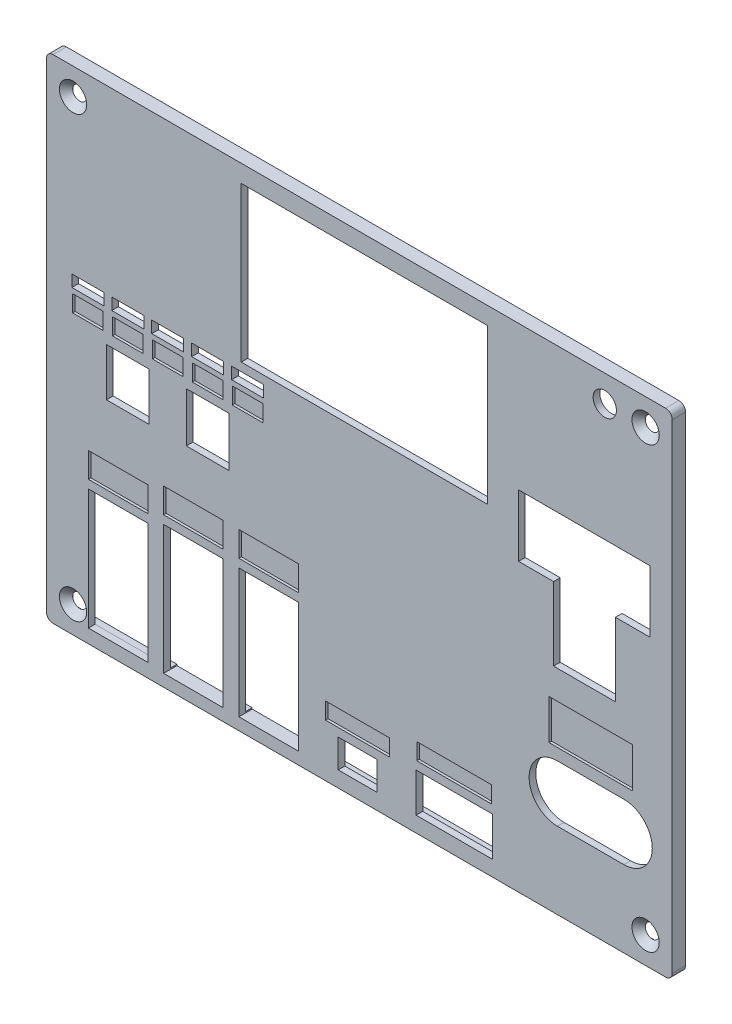
SolidWorks part; units mm, degrees
ref_plane "Alzado" through (0, 0, 0) normal (0, 0, 1) x (1, 0, 0)
ref_plane "Planta" through (0, 0, 0) normal (0, 1, 0) x (1, 0, 0)
ref_plane "Vista lateral" through (0, 0, 0) normal (1, 0, 0) x (0, 0, -1)
sketch "Croquis1" plane through (0, 0, 0) normal (0, 0, 1) x (1, 0, 0)
  line L1 (0, 0) -> (188, 0)
  line L2 (0, 0) -> (0, 148)
  line L3 (0, 148) -> (188, 148)
  line L4 (188, 0) -> (188, 148)
  dimension "D1" = 148
  dimension "D2" = 188
extrude "Saliente-Extruir1" add sketch "Croquis1" along normal blind 4
ref_plane "Plano1" through (0, 0, 0) normal (0, 0, -1) x (-1, 0, 0)
sketch "Croquis2" plane through (0, 0, 0) normal (0, 0, -1) x (-1, 0, 0)
  line L0 (-188, 148) -> (0, 148) construction
  line L1 (-180, 140) -> (-8, 140)
  line L2 (-180, 140) -> (-180, 8)
  line L3 (-180, 8) -> (-8, 8)
  line L4 (-8, 140) -> (-8, 8)
  line L5 (-188, 0) -> (-188, 148) construction
  line L6 (0, 0) -> (-188, 0) construction
  line L7 (0, 148) -> (0, 0) construction
  circle A0 centre (-8, 140) radius 2.1
  circle A1 centre (-180, 140) radius 2.1
  circle A2 centre (-180, 8) radius 2.1
  circle A3 centre (-8, 8) radius 2.1
  dimension "D5" = 4.2
  dimension "D6" = 4.2
  dimension "D7" = 4.2
  dimension "D8" = 4.2
  dimension "D1" = 8
  dimension "D2" = 8
  dimension "D3" = 8
  dimension "D4" = 8
extrude "Cortar-Extruir1" cut sketch "Croquis2" against normal blind 4 contours A0 | A1 | A2 | A3
fillet "Redondeo1" radius 2 4 edges at (0, 0, 2) (188, 0, 2) (188, 148, 2) (0, 148, 2)
chamfer "Chaflán1" distance 2 angle 45 4 edges at (5.9, 8, 4) (177.9, 8, 4) (177.9, 140, 4) (5.9, 140, 4)
sketch "Croquis3" plane through (0, 0, 0) normal (0, 0, -1) x (-1, 0, 0)
  line L0 (-184, 144) -> (-4, 144) construction
  line L1 (-4, 144) -> (-4, 4) construction
  line L2 (-4, 4) -> (-184, 4) construction
  line L3 (-184, 4) -> (-184, 144) construction
  line L4 (-186, 148) -> (-2, 148) construction
  line L5 (-188, 2) -> (-188, 146) construction
  line L6 (0, 146) -> (0, 2) construction
  line L7 (-2, 0) -> (-186, 0) construction
  dimension "D1" = 4
  dimension "D2" = 4
  dimension "D3" = 4
  dimension "D4" = 4
sketch "Croquis4" plane through (0, 0, 4) normal (0, 0, 1) x (1, 0, 0)
  line L0 (28.25, 93.27) -> (20.63, 93.27) construction
  line L1 (12.6, 40.31) -> (30.5, 40.31)
  line L2 (12.6, 40.31) -> (12.6, 4.11)
  line L3 (12.6, 4.11) -> (30.5, 4.11)
  line L4 (30.5, 40.31) -> (30.5, 4.11)
  line L5 (31.63, 93.77) -> (41.25, 93.77)
  line L6 (31.63, 93.77) -> (31.63, 90.23)
  line L7 (15.1, 5.61) -> (28, 5.61) construction
  line L8 (14.1, 31.91) -> (14.1, 6.61) construction
  line L9 (29, 6.61) -> (29, 37.81) construction
  line L10 (28, 38.81) -> (17.3, 38.81) construction
  line L11 (37.7, 5.13) -> (50.6, 5.13) construction
  line L12 (35.2, 42.37) -> (53.1, 42.37)
  line L13 (35.2, 42.37) -> (35.2, 3.63)
  line L14 (35.2, 3.63) -> (53.1, 3.63)
  line L15 (53.1, 42.37) -> (53.1, 3.63)
  line L16 (51.6, 6.13) -> (51.6, 39.87) construction
  line L17 (36.7, 33.97) -> (36.7, 6.13) construction
  line L18 (50.6, 40.87) -> (39.9, 40.87) construction
  line L19 (73.22, 40.87) -> (62.52, 40.87) construction
  line L20 (57.82, 42.37) -> (75.72, 42.37)
  line L21 (57.82, 42.37) -> (57.82, 3.63)
  line L22 (57.82, 3.63) -> (75.72, 3.63)
  line L23 (75.72, 42.37) -> (75.72, 3.63)
  line L24 (59.32, 8.58) -> (59.32, 39.87) construction
  line L25 (74.22, 6.13) -> (74.22, 39.87) construction
  line L26 (60.32, 5.13) -> (73.22, 5.13) construction
  line L27 (31.63, 90.23) -> (41.25, 90.23)
  line L28 (94.476, 11.27) -> (92.444, 11.27) construction
  line L29 (87.65, 13.27) -> (99.27, 13.27)
  line L30 (87.65, 13.27) -> (87.65, 4.73)
  line L31 (87.65, 4.73) -> (99.27, 4.73)
  line L32 (99.27, 13.27) -> (99.27, 4.73)
  line L33 (97.27, 8.984) -> (97.27, 11.016) construction
  line L34 (89.65, 11.016) -> (89.65, 8.984) construction
  line L35 (92.444, 8.73) -> (94.476, 8.73) construction
  line L36 (129.95, 9.5) -> (129.95, 13.4) construction
  line L37 (111.05, 16.4) -> (133.95, 16.4)
  line L38 (111.05, 16.4) -> (111.05, 4.65)
  line L39 (111.05, 4.65) -> (133.95, 4.65)
  line L40 (133.95, 16.4) -> (133.95, 4.65)
  line L41 (115.05, 13.4) -> (115.05, 9.5) construction
  line L42 (118.5, 7.65) -> (126.5, 7.65) construction
  line L43 (129.95, 13.4) -> (115.05, 13.4) construction
  line L44 (41.25, 93.77) -> (41.25, 90.23)
  line L45 (16.25, 93.27) -> (8.63, 93.27) construction
  line L46 (7.63, 93.77) -> (17.25, 93.77)
  line L47 (7.63, 93.77) -> (7.63, 90.23)
  line L48 (7.63, 90.23) -> (17.25, 90.23)
  line L49 (17.25, 93.77) -> (17.25, 90.23)
  line L50 (8.63, 90.73) -> (16.25, 90.73) construction
  line L51 (8.63, 93.27) -> (8.63, 90.73) construction
  line L52 (16.25, 90.73) -> (16.25, 93.27) construction
  line L53 (43.63, 93.77) -> (53.25, 93.77)
  line L54 (19.63, 93.77) -> (29.25, 93.77)
  line L55 (19.63, 93.77) -> (19.63, 90.23)
  line L56 (19.63, 90.23) -> (29.25, 90.23)
  line L57 (29.25, 93.77) -> (29.25, 90.23)
  line L58 (43.63, 93.77) -> (43.63, 90.23)
  line L59 (43.63, 90.23) -> (53.25, 90.23)
  line L60 (53.25, 93.77) -> (53.25, 90.23)
  line L61 (55.63, 93.77) -> (65.25, 93.77)
  line L62 (55.63, 93.77) -> (55.63, 90.23)
  line L63 (55.63, 90.23) -> (65.25, 90.23)
  line L64 (65.25, 93.77) -> (65.25, 90.23)
  line L65 (20.63, 93.27) -> (20.63, 90.73) construction
  line L66 (20.63, 90.73) -> (28.25, 90.73) construction
  line L67 (28.25, 90.73) -> (28.25, 93.27) construction
  line L68 (40.25, 93.27) -> (32.63, 93.27) construction
  line L69 (32.63, 93.27) -> (32.63, 90.73) construction
  line L70 (32.63, 90.73) -> (40.25, 90.73) construction
  line L71 (40.25, 90.73) -> (40.25, 93.27) construction
  line L72 (44.63, 93.27) -> (44.63, 90.73) construction
  line L73 (52.25, 93.27) -> (44.63, 93.27) construction
  line L74 (44.63, 90.73) -> (52.25, 90.73) construction
  line L75 (52.25, 90.73) -> (52.25, 93.27) construction
  line L76 (64.25, 93.27) -> (56.63, 93.27) construction
  line L77 (56.63, 93.27) -> (56.63, 90.73) construction
  line L78 (56.63, 90.73) -> (64.25, 90.73) construction
  line L79 (64.25, 90.73) -> (64.25, 93.27) construction
  line L80 (131.02, 141.25) -> (60.02, 141.25) construction
  line L81 (58.52, 142.75) -> (132.52, 142.75)
  line L82 (58.52, 142.75) -> (58.52, 96.25)
  line L83 (58.52, 96.25) -> (132.52, 96.25)
  line L84 (132.52, 142.75) -> (132.52, 96.25)
  line L85 (60.02, 141.25) -> (60.02, 97.75) construction
  line L86 (60.02, 97.75) -> (89.52, 97.75) construction
  line L87 (131.02, 97.75) -> (131.02, 141.25) construction
  line L88 (23.675, 79.6) -> (25.175, 79.6) construction
  line L89 (18.025, 80.6) -> (30.825, 80.6)
  line L90 (18.025, 80.6) -> (18.025, 66.2)
  line L91 (18.025, 66.2) -> (30.825, 66.2)
  line L92 (30.825, 80.6) -> (30.825, 66.2)
  line L93 (29.325, 75) -> (29.325, 70) construction
  line L94 (19.525, 70) -> (19.525, 75) construction
  line L95 (20.675, 67.7) -> (26.85, 67.7) construction
  line L96 (47.675, 79.6) -> (49.175, 79.6) construction
  line L97 (42.025, 81.1) -> (54.825, 81.1)
  line L98 (42.025, 81.1) -> (42.025, 66.2)
  line L99 (42.025, 66.2) -> (54.825, 66.2)
  line L100 (54.825, 81.1) -> (54.825, 66.2)
  line L101 (53.325, 75) -> (53.325, 70) construction
  line L102 (44.675, 67.7) -> (50.85, 67.7) construction
  line L103 (43.525, 70) -> (43.525, 75) construction
  line L105 (141.84, 104.68) -> (181.39, 104.68)
  line L109 (145.265, 103.18) -> (148.44, 103.18) construction
  line L112 (153.5, 31.5) -> (173.5, 31.5) construction
  line L113 (153.5, 31.5) -> (173.5, 31.5) construction
  line L114 (153.5, 40) -> (173.5, 40)
  line L115 (153.5, 23) -> (173.5, 23)
  line L116 (141.84, 104.68) -> (141.84, 86.08)
  line L117 (141.84, 86.08) -> (152.34, 86.08)
  line L118 (152.34, 86.08) -> (152.34, 64.08)
  line L119 (152.34, 64.08) -> (170.94, 64.08)
  line L120 (170.94, 64.08) -> (170.94, 86.08)
  line L121 (170.94, 86.08) -> (181.39, 86.08)
  line L122 (181.39, 86.08) -> (181.39, 104.68)
  line L123 (143.34, 102.38) -> (143.34, 101.18) construction
  line L124 (145.265, 87.58) -> (148.44, 87.58) construction
  line L125 (153.84, 80.38) -> (153.84, 79.18) construction
  line L126 (155.765, 65.58) -> (158.94, 65.58) construction
  line L127 (169.44, 79.18) -> (169.44, 80.38) construction
  line L128 (174.79, 87.58) -> (177.965, 87.58) construction
  line L129 (179.89, 89.58) -> (179.89, 88.38) construction
  arc A0 (153.5, 40) -> (153.5, 23) centre (153.5, 31.5) ccw
  arc A1 (173.5, 23) -> (173.5, 40) centre (173.5, 31.5) ccw
  circle A2 centre (167.73, 140) radius 3.5
  point P68 (12.44, 90.73)
  point P141 (18.025, 73.4)
  point P174 (163.5, 31.5)
  point P192 (176.3775, 87.58)
  dimension "D57" = 17
  dimension "D58" = 7
  dimension "D1" = 1.5
  dimension "D2" = 1.5
  dimension "D3" = 1.5
  dimension "D4" = 1.5
  dimension "D5" = 1.5
  dimension "D6" = 1.5
  dimension "D7" = 1.5
  dimension "D8" = 1.5
  dimension "D9" = 1.5
  dimension "D10" = 1.5
  dimension "D11" = 1.5
  dimension "D12" = 1.5
  dimension "D13" = 2
  dimension "D14" = 2
  dimension "D15" = 2
  dimension "D16" = 4
  dimension "D17" = 4
  dimension "D18" = 4
  dimension "D19" = 3
  dimension "D20" = 3
  dimension "D21" = 0.5
  dimension "D22" = 0.5
  dimension "D23" = 1
  dimension "D24" = 1
  dimension "D25" = 0.5
  dimension "D26" = 1
  dimension "D27" = 0.5
  dimension "D28" = 1
  dimension "D29" = 0.5
  dimension "D30" = 1
  dimension "D31" = 0.5
  dimension "D32" = 1
  dimension "D33" = 1
  dimension "D34" = 0.5
  dimension "D35" = 0.5
  dimension "D36" = 1
  dimension "D37" = 0.5
  dimension "D38" = 1
  dimension "D39" = 0.5
  dimension "D40" = 1
  dimension "D41" = 1.5
  dimension "D42" = 1.5
  dimension "D43" = 1.5
  dimension "D44" = 1.5
  dimension "D45" = 1
  dimension "D46" = 1.5
  dimension "D47" = 1.5
  dimension "D48" = 1.5
  dimension "D49" = 1.5
  dimension "D50" = 1.5
  dimension "D51" = 1.5
  dimension "D52" = 1.5
  dimension "D53" = 1.5
  dimension "D54" = 1.5
  dimension "D55" = 1.5
  dimension "D56" = 1.5
  dimension "D59" = 1.5
  dimension "D60" = 1.5
  dimension "D61" = 1.5
  dimension "D62" = 1.5
extrude "Cortar-Extruir4" cut sketch "Croquis4" against normal up to next
sketch "Croquis5" plane through (0, 0, 0) normal (0, 0, -1) x (-1, 0, 0)
  line L1 (-4, 144) -> (-184, 144)
  line L2 (-4, 144) -> (-4, 4)
  line L3 (-4, 4) -> (-184, 4)
  line L4 (-184, 144) -> (-184, 4)
extrude "Cortar-Extruir5" cut sketch "Croquis5" against normal blind 2
sketch "Croquis7" plane through (0, 0, 0) normal (0, 0, -1) x (-1, 0, 0)
  line L0 (0, 74) -> (-4, 74) construction
  line L1 (-186, 61.5) -> (-186, 86.5) construction
  line L3 (-2, 61.5) -> (-2, 86.5) construction
  line L6 (0, 146) -> (0, 2) construction
  line L7 (-4, 144) -> (-4, 4) construction
  line L8 (-188, 74) -> (-184, 74) construction
  line L9 (-188, 2) -> (-188, 146) construction
  line L10 (-184, 4) -> (-184, 144) construction
  line L16 (-186.5, 61.5) -> (-186.5, 86.5)
  line L17 (-185.5, 61.5) -> (-185.5, 86.5)
  line L18 (-2.5, 61.5) -> (-2.5, 86.5)
  line L19 (-1.5, 61.5) -> (-1.5, 86.5)
  arc A8 (-186.5, 61.5) -> (-185.5, 61.5) centre (-186, 61.5) ccw
  arc A9 (-185.5, 86.5) -> (-186.5, 86.5) centre (-186, 86.5) ccw
  arc A10 (-2.5, 61.5) -> (-1.5, 61.5) centre (-2, 61.5) ccw
  arc A11 (-1.5, 86.5) -> (-2.5, 86.5) centre (-2, 86.5) ccw
  point P8 (-2, 74)
  point P22 (-186, 74)
  dimension "D1" = 25
  dimension "D2" = 1
  dimension "D3" = 25
  dimension "D4" = 1
extrude "Saliente-Extruir4" add sketch "Croquis7" along normal blind 1.5
ref_plane "Plano2" through (0, 0, 4) normal (0, 0, 1) x (1, 0, 0)
sketch "Croquis8" plane through (0, 0, 4) normal (0, 0, 1) x (1, 0, 0)
  line L0 (14.1, 9.06) -> (14.1, 37.81) construction
  line L1 (12.6, 50.31) -> (30.5, 50.31)
  line L2 (12.6, 50.31) -> (12.6, 42.81)
  line L3 (12.6, 42.81) -> (30.5, 42.81)
  line L4 (30.5, 50.31) -> (30.5, 42.81)
  line L5 (29, 6.61) -> (29, 37.81) construction
  line L6 (30.5, 40.31) -> (12.6, 40.31) construction
  line L7 (53.1, 42.37) -> (35.2, 42.37) construction
  line L8 (35.2, 52.37) -> (53.1, 52.37)
  line L9 (35.2, 52.37) -> (35.2, 44.87)
  line L10 (35.2, 44.87) -> (53.1, 44.87)
  line L11 (53.1, 52.37) -> (53.1, 44.87)
  line L12 (36.7, 8.58) -> (36.7, 39.87) construction
  line L13 (51.6, 6.13) -> (51.6, 39.87) construction
  line L14 (75.72, 42.37) -> (57.82, 42.37) construction
  line L15 (57.82, 52.37) -> (75.72, 52.37)
  line L16 (57.82, 52.37) -> (57.82, 44.87)
  line L17 (57.82, 44.87) -> (75.72, 44.87)
  line L18 (75.72, 52.37) -> (75.72, 44.87)
  line L19 (74.22, 6.13) -> (74.22, 39.87) construction
  line L20 (59.32, 8.58) -> (59.32, 39.87) construction
  line L21 (32.63, 93.27) -> (32.63, 90.73) construction
  line L22 (99.27, 13.27) -> (87.65, 13.27) construction
  line L23 (83.85, 20.77) -> (103.07, 20.77)
  line L24 (83.85, 20.77) -> (83.85, 15.77)
  line L25 (83.85, 15.77) -> (103.07, 15.77)
  line L26 (103.07, 20.77) -> (103.07, 15.77)
  line L27 (87.65, 13.27) -> (87.65, 4.73) construction
  line L28 (99.27, 4.73) -> (99.27, 13.27) construction
  line L29 (133.95, 16.4) -> (111.05, 16.4) construction
  line L30 (111.25, 23.9) -> (133.75, 23.9)
  line L31 (111.25, 23.9) -> (111.25, 18.9)
  line L32 (111.25, 18.9) -> (133.75, 18.9)
  line L33 (133.75, 23.9) -> (133.75, 18.9)
  line L34 (40.25, 90.73) -> (40.25, 93.27) construction
  line L35 (44.63, 93.27) -> (44.63, 90.73) construction
  line L36 (115.05, 13.4) -> (115.05, 9.5) construction
  line L37 (129.95, 9.5) -> (129.95, 13.4) construction
  line L38 (7.63, 90.23) -> (17.25, 90.23) construction
  line L39 (151, 55.5) -> (176, 55.5)
  line L40 (151, 55.5) -> (151, 43.5)
  line L41 (151, 43.5) -> (176, 43.5)
  line L42 (176, 55.5) -> (176, 43.5)
  line L43 (7.83, 88.73) -> (17.05, 88.73)
  line L44 (7.83, 88.73) -> (7.83, 83.73)
  line L45 (7.83, 83.73) -> (17.05, 83.73)
  line L46 (17.05, 88.73) -> (17.05, 83.73)
  line L47 (19.83, 88.73) -> (29.05, 88.73)
  line L48 (19.83, 88.73) -> (19.83, 83.73)
  line L49 (19.83, 83.73) -> (29.05, 83.73)
  line L50 (29.05, 88.73) -> (29.05, 83.73)
  line L51 (31.83, 88.73) -> (41.0528, 88.73)
  line L52 (31.83, 88.73) -> (31.83, 83.73)
  line L53 (31.83, 83.73) -> (41.0528, 83.73)
  line L54 (41.0528, 88.73) -> (41.0528, 83.73)
  line L55 (43.83, 88.73) -> (53.05, 88.73)
  line L56 (43.83, 88.73) -> (43.83, 83.73)
  line L57 (43.83, 83.73) -> (53.05, 83.73)
  line L58 (53.05, 88.73) -> (53.05, 83.73)
  line L59 (55.83, 88.73) -> (65.05, 88.73)
  line L60 (55.83, 88.73) -> (55.83, 83.73)
  line L61 (55.83, 83.73) -> (65.05, 83.73)
  line L62 (65.05, 88.73) -> (65.05, 83.73)
  line L63 (52.25, 90.73) -> (52.25, 93.27) construction
  line L65 (8.63, 93.27) -> (8.63, 90.73) construction
  line L66 (16.25, 90.73) -> (16.25, 93.27) construction
  line L67 (19.63, 90.23) -> (29.25, 90.23) construction
  line L68 (20.63, 93.27) -> (20.63, 90.73) construction
  line L69 (28.25, 90.73) -> (28.25, 93.27) construction
  line L70 (31.63, 90.23) -> (41.25, 90.23) construction
  line L72 (43.63, 90.23) -> (53.25, 90.23) construction
  line L73 (55.63, 90.23) -> (65.25, 90.23) construction
  line L74 (64.25, 90.73) -> (64.25, 93.27) construction
  line L75 (56.63, 93.27) -> (56.63, 90.73) construction
  circle A0 centre (153.5, 31.5) radius 2.5 construction
  circle A1 centre (173.5, 31.5) radius 2.5 construction
  point P50 (129.95, 11.45)
  dimension "D24" = 2.5
  dimension "D1" = 7.5
  dimension "D2" = 1.5
  dimension "D3" = 1.5
  dimension "D4" = 2.5
  dimension "D5" = 2.5
  dimension "D6" = 7.5
  dimension "D7" = 1.5
  dimension "D8" = 1.5
  dimension "D9" = 7.5
  dimension "D10" = 2.5
  dimension "D11" = 1.5
  dimension "D12" = 1.5
  dimension "D13" = 2.5
  dimension "D14" = 3.8
  dimension "D15" = 3.8
  dimension "D16" = 5
  dimension "D17" = 2.5
  dimension "D18" = 3.8
  dimension "D19" = 3.8
  dimension "D20" = 5
  dimension "D21" = 12
  dimension "D22" = 12
  dimension "D23" = 2.5
  dimension "D25" = 1.5
  dimension "D26" = 0.8
  dimension "D27" = 0.8
  dimension "D28" = 5
  dimension "D29" = 1.5
  dimension "D30" = 5
  dimension "D31" = 0.8
  dimension "D32" = 0.8
  dimension "D33" = 1.5
  dimension "D34" = 0.8
  dimension "D35" = 5
  dimension "D36" = 0.8028
  dimension "D37" = 0.8
  dimension "D38" = 0.8
  dimension "D39" = 1.5
  dimension "D40" = 5
  dimension "D41" = 1.5
  dimension "D42" = 5
  dimension "D43" = 0.8
  dimension "D44" = 0.8
extrude "Cortar-Extruir6" cut sketch "Croquis8" against normal blind 0.75
equation "\"D2@Croquis2\"=\"D1@Croquis2\""
equation "\"D3@Croquis2\"=\"D1@Croquis2\""
equation "\"D4@Croquis2\"=\"D1@Croquis2\""
equation "\"D6@Croquis2\"=\"D5@Croquis2\""
equation "\"D7@Croquis2\"=\"D5@Croquis2\""
equation "\"D8@Croquis2\"=\"D5@Croquis2\""
equation "\"D2@Croquis3\"=\"D1@Croquis3\""
equation "\"D3@Croquis3\"=\"D1@Croquis3\""
equation "\"D4@Croquis3\"=\"D1@Croquis3\""
